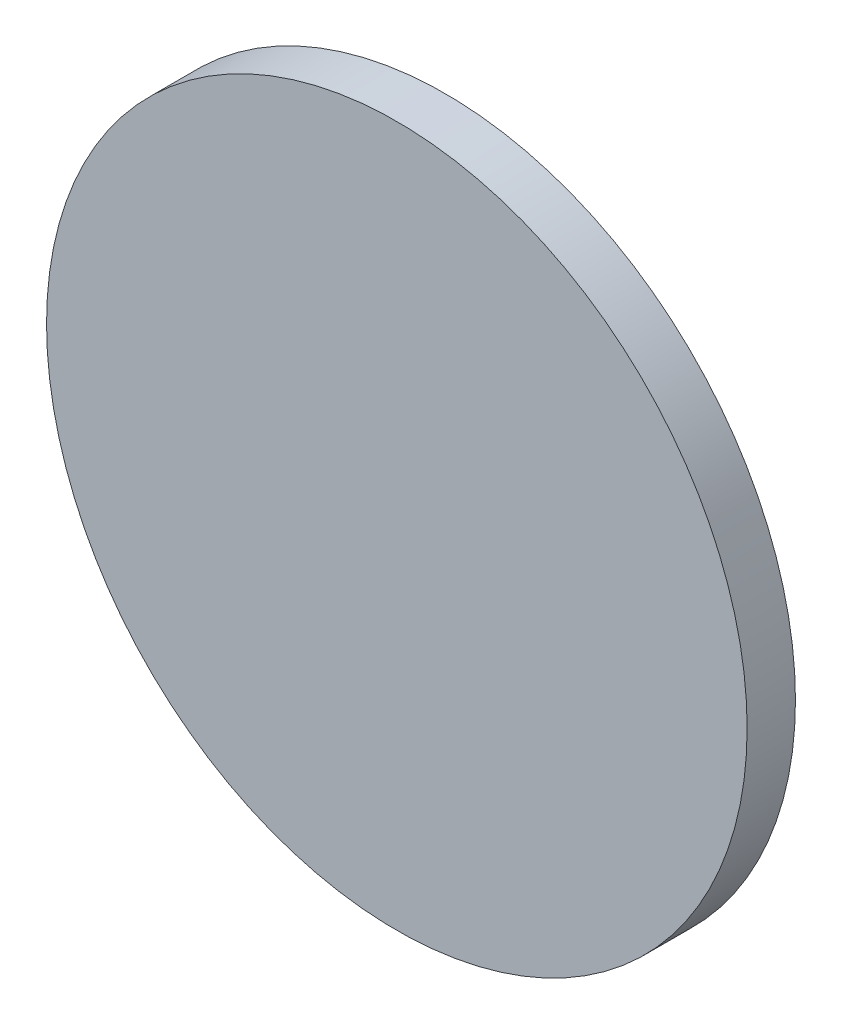
SolidWorks part; units mm, degrees
ref_plane "Front Plane" through (0, 0, 0) normal (0, 0, 1) x (1, 0, 0)
ref_plane "Top Plane" through (0, 0, 0) normal (0, 1, 0) x (1, 0, 0)
ref_plane "Right Plane" through (0, 0, 0) normal (1, 0, 0) x (0, 0, -1)
sketch "Sketch1" plane through (0, 0, 0) normal (0, 0, 1) x (1, 0, 0)
  circle A0 centre (0, 0) radius 14.5
  dimension "D1" = 29
extrude "Boss-Extrude1" add sketch "Sketch1" along normal blind 2
